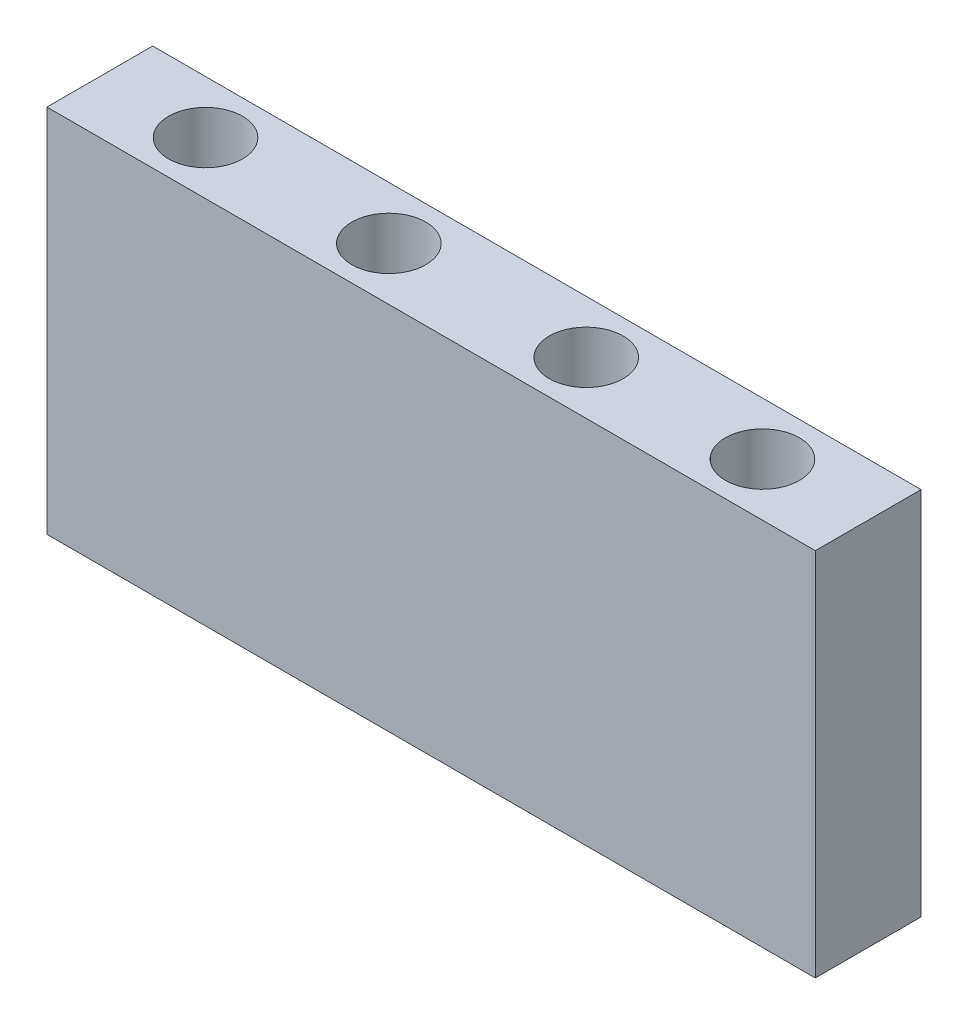
SolidWorks part; units mm, degrees
material "Glas"
ref_plane "Ebene vorne" through (0, 0, 0) normal (0, 0, 1) x (1, 0, 0)
ref_plane "Ebene oben" through (0, 0, 0) normal (0, 1, 0) x (1, 0, 0)
ref_plane "Ebene rechts" through (0, 0, 0) normal (1, 0, 0) x (0, 0, -1)
sketch "Skizze1" plane through (0, 0, 0) normal (0, 0, 1) x (1, 0, 0)
  line L1 (0, 0) -> (218, 0)
  line L2 (0, 0) -> (0, 105)
  line L3 (0, 105) -> (218, 105)
  line L4 (218, 0) -> (218, 105)
  dimension "D1" = 218
  dimension "D2" = 105
extrude "Aufsatz-Linear austragen1" add sketch "Skizze1" along normal blind 30
sketch "Skizze11" plane through (0, 105, 0) normal (0, 1, 0) x (1, 0, 0)
  line L1 (218, -30) -> (218, 0) construction
  line L2 (0, -30) -> (0, 0) construction
  circle A0 centre (30, -15) radius 10.5
  circle A1 centre (82, -15) radius 10.5
  circle A2 centre (138, -15) radius 10.5
  circle A3 centre (188, -15) radius 10.5
  dimension "D1" = 21
  dimension "D2" = 21
  dimension "D3" = 21
  dimension "D4" = 21
  dimension "D5" = 30
  dimension "D6" = 30
  dimension "D7" = 50
  dimension "D8" = 52
extrude "Schnitt-Linear austragen2" cut sketch "Skizze11" against normal through all
ref_plane "Ebene1" through (0, 105, 0) normal (0, 0, -1) x (-1, 0, 0)
sketch "Skizze12" plane through (0, 105, 0) normal (0, 0, -1) x (-1, 0, 0)
